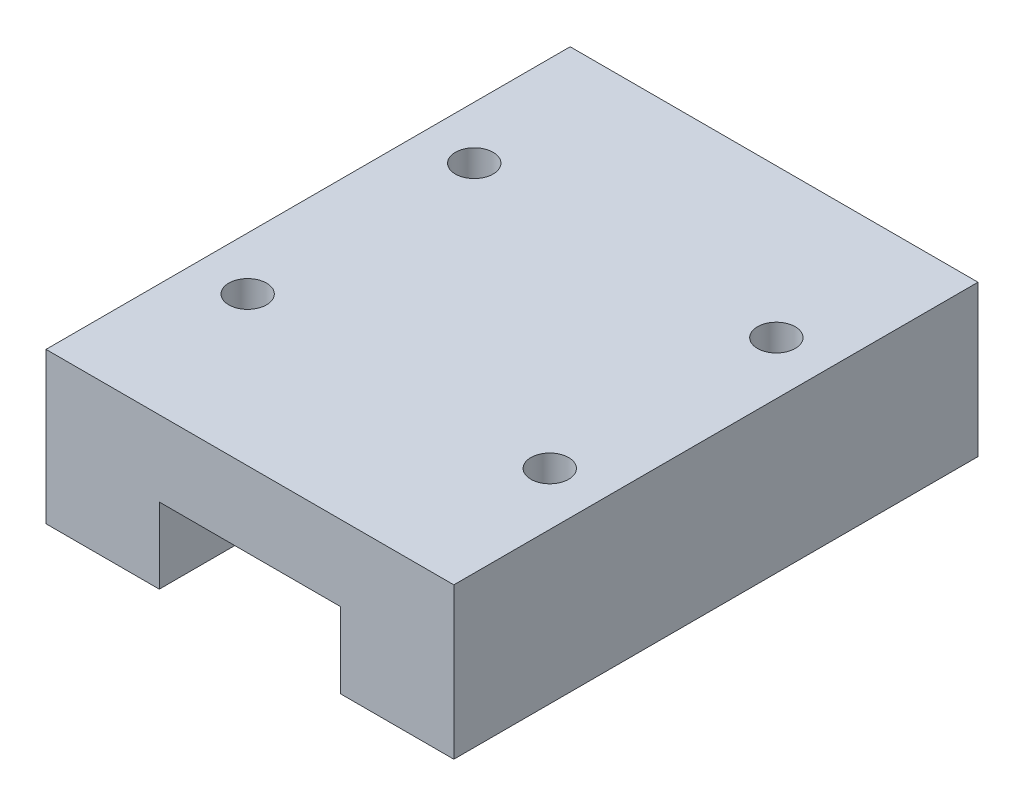
SolidWorks part; units mm, degrees
ref_plane "Front" through (0, 0, 0) normal (0, 0, 1) x (1, 0, 0)
ref_plane "Top" through (0, 0, 0) normal (0, 1, 0) x (1, 0, 0)
ref_plane "Right" through (0, 0, 0) normal (1, 0, 0) x (0, 0, -1)
sketch "Sketch2" plane through (0, 0, 0) normal (0, 0, 1) x (1, 0, 0)
  line L0 (0, 0) -> (0, 10)
  line L1 (0, 10) -> (27, 10)
  line L2 (27, 10) -> (27, 0)
  line L3 (27, 0) -> (19.5, 0)
  line L4 (19.5, 0) -> (19.5, 5)
  line L5 (19.5, 5) -> (7.5, 5)
  line L6 (7.5, 5) -> (7.5, 0)
  line L7 (7.5, 0) -> (0, 0)
  dimension "D1" = 27
  dimension "D2" = 10
  dimension "D3" = 7.5
  dimension "D4" = 5
extrude "Boss-Extrude1" add sketch "Sketch2" along normal blind 34.7
hole_wizard "M3x0.5 Tapped Hole1" positions "Sketch3" profile "Sketch4" tap size "M3x0.5" standard "ANSI Metric"
sketch "Sketch3" plane through (0, 10, 0) normal (0, 1, 0) x (1, 0, 0)
  line L0 (0, -17.35) -> (27, -17.35) construction
  line L1 (0, -34.7) -> (0, 0) construction
  line L2 (27, -34.7) -> (27, 0) construction
  line L5 (13.5, 0) -> (13.5, -34.7) construction
  line L6 (27, 0) -> (0, 0) construction
  line L7 (27, -34.7) -> (0, -34.7) construction
  point P16 (3.5, -9.85)
  point P18 (3.5, -24.85)
  point P20 (23.5, -24.85)
  point P22 (23.5, -9.85)
  dimension "D1" = 15
  dimension "D2" = 20
  dimension "D3" = 10
  dimension "D4" = 7.5
  dimension "D5" = 15
  dimension "D6" = 20
  dimension "D7" = 7.5
cosmetic thread "Hole Thread1" parameters "D1"=2.4, "D2"=3
cosmetic thread "Hole Thread2" parameters "D1"=2.4, "D2"=3
cosmetic thread "Hole Thread3" parameters "D1"=2.4, "D2"=3
cosmetic thread "Hole Thread4" parameters "D1"=2.4, "D2"=3
sketch "Sketch4" plane through (23.5, 10, 9.85) normal (1, 0, 0) x (0, 0, 1)
  line L0 (0, 0) -> (0, 6.7511)
  line L1 (0, 6.7511) -> (1.25, 6)
  line L2 (1.25, 6) -> (1.25, 0)
  line L5 (1.25, 0) -> (0, 0)
  line L10 (0, 6.7511) -> (-1.25, 6) construction
  line L11 (0, -6.35) -> (0, 107.95) construction
  dimension "Tap Drill Dia." = 2.5
  dimension "Tap Drill Depth" = 6
  dimension "Drill Angle" = 118
sketch "Sketch5" plane through (0, 10, 0) normal (0, 1, 0) x (1, 0, 0)
  circle A0 centre (23.5, -24.85) radius 3
  circle A1 centre (23.5, -9.85) radius 3
  circle A2 centre (3.5, -9.85) radius 3
  circle A3 centre (3.5, -24.85) radius 3
  circle A4 centre (3.5, -9.85) radius 2.85
  circle A5 centre (23.5, -9.85) radius 2.85
  circle A6 centre (3.5, -24.85) radius 2.85
  circle A7 centre (23.5, -24.85) radius 2.85
  dimension "D1" = 6
  dimension "D2" = 5.7
